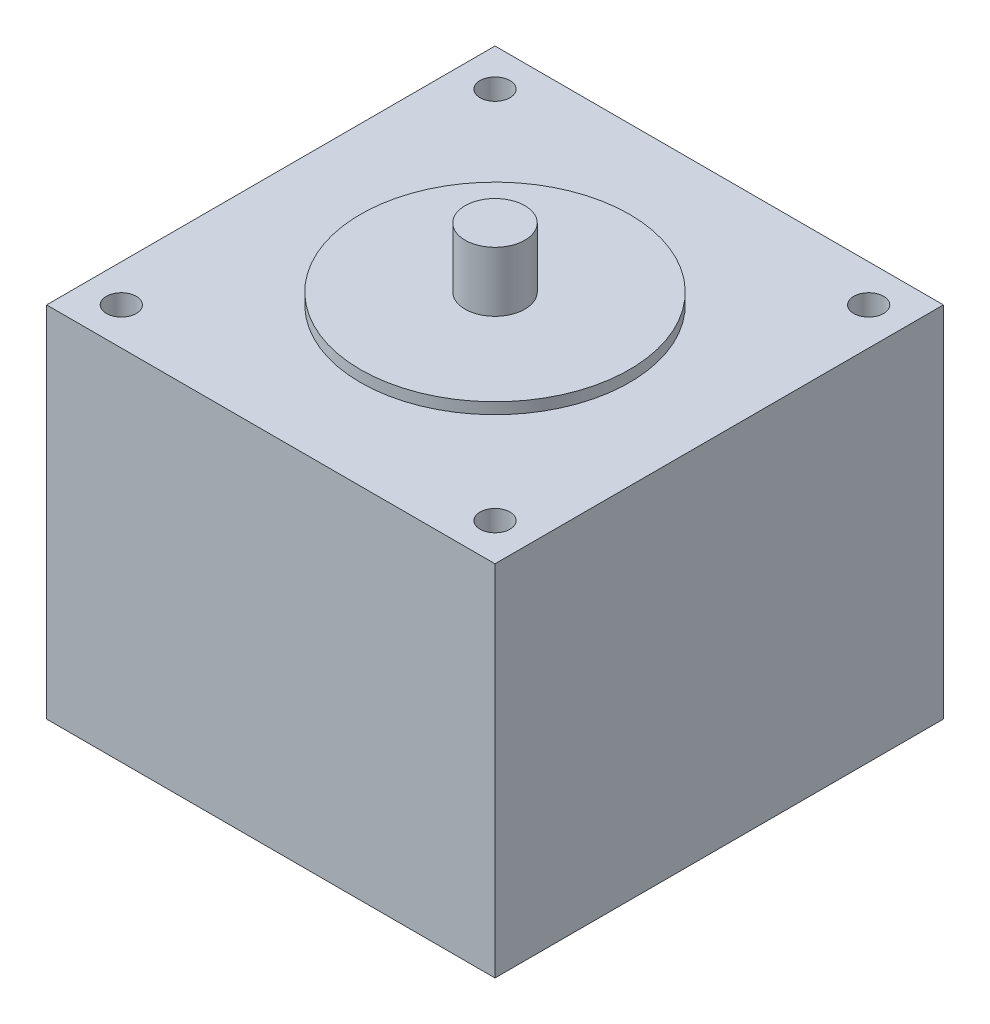
SolidWorks part; units mm, degrees
ref_plane "Front Plane" through (0, 0, 0) normal (0, 0, 1) x (1, 0, 0)
ref_plane "Top Plane" through (0, 0, 0) normal (0, 1, 0) x (1, 0, 0)
ref_plane "Right Plane" through (0, 0, 0) normal (1, 0, 0) x (0, 0, -1)
sketch "Sketch1" plane through (0, 0, 0) normal (0, 1, 0) x (1, 0, 0)
  line L0 (-25, 25) -> (-25, -25) construction
  line L1 (30, 30) -> (-30, 30)
  line L2 (30, 30) -> (30, -30)
  line L3 (30, -30) -> (-30, -30)
  line L4 (-30, 30) -> (-30, -30)
  line L5 (30, 30) -> (-30, -30) construction
  line L6 (30, -30) -> (-30, 30) construction
  line L7 (25, -25) -> (-25, -25) construction
  line L8 (25, 25) -> (25, -25) construction
  line L9 (25, 25) -> (-25, 25) construction
  circle A0 centre (-25, 25) radius 2
  circle A1 centre (25, 25) radius 2
  circle A2 centre (25, -25) radius 2
  circle A3 centre (-25, -25) radius 2
  point P0 (0, 0)
  dimension "D3" = 4
  dimension "D1" = 60
  dimension "D2" = 5
extrude "Boss-Extrude1" add sketch "Sketch1" along normal blind 48
sketch "Sketch3" plane through (0, 0, 0) normal (0, 0, 1) x (1, 0, 0)
  line L0 (0, 48) -> (18, 48)
  line L1 (-30, 48) -> (30, 48) construction
  line L2 (18, 48) -> (18, 49.5)
  line L3 (18, 49.5) -> (4, 49.5)
  line L4 (4, 49.5) -> (4, 57.5)
  line L5 (4, 57.5) -> (0, 57.5)
  line L6 (0, 57.5) -> (0, 48)
  dimension "D1" = 18
  dimension "D2" = 1.5
  dimension "D3" = 14
  dimension "D4" = 8
revolve "Revolve1" add sketch "Sketch3" angle 360 about L6
